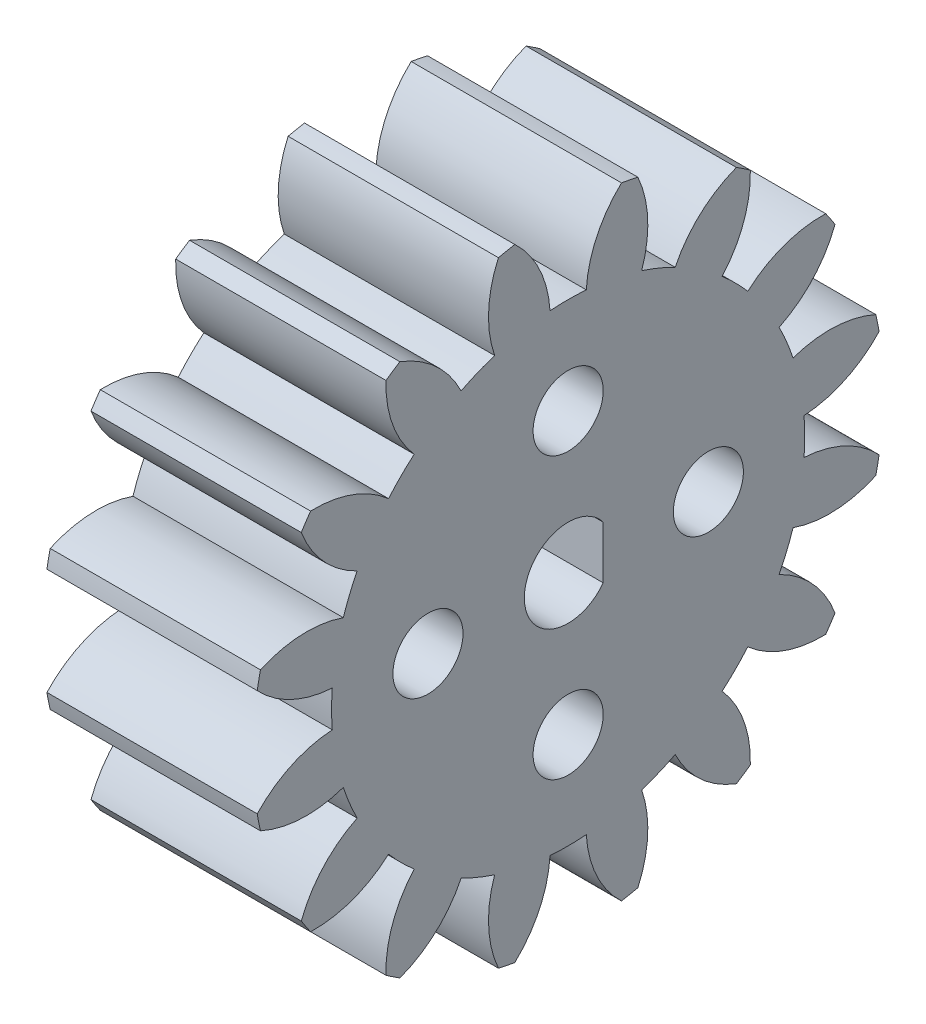
SolidWorks part; units mm, degrees
ref_plane "Plane1" through (0, 0, 0) normal (0, 0, 1) x (1, 0, 0)
ref_plane "Plane2" through (0, 0, 0) normal (0, 1, 0) x (1, 0, 0)
ref_plane "Plane3" through (0, 0, 0) normal (1, 0, 0) x (0, 0, -1)
sketch "HoldingSke" plane through (0, 0, 0) normal (0, 1, 0) x (1, 0, 0)
  line L0 (0, 0) -> (0.4806, -0.1378)
  line L1 (-15, 0) -> (100, 0) construction
  line L2 (0, 0) -> (-2.1039, 2.3779)
  line L3 (0, 0) -> (-11.863, 4.5341)
  line L4 (0, 0) -> (8.3015, 2.3804)
  line L5 (0, 0) -> (-46.8476, -17.4728)
  line L6 (0, 0) -> (-9.9476, -6.7116)
  line L7 (-2.1039, 2.3779) -> (8.6586, 51.2059)
  line L8 (-76.2, 54.61) -> (-75.5, 54.61)
  line L9 (-71.009, 38.7566) -> (-53.1078, 45.2721)
  line L10 (-76.2, 71.12) -> (104.1128, 71.12)
  line L11 (0, 0) -> (-12, 0)
  line L12 (-76.2, 101.6) -> (-76.133, 101.6)
  line L13 (24.9733, 27.94) -> (52.9518, 28.4284)
  line L14 (24.9733, 27.94) -> (24.9743, 27.94)
  line L15 (24.9733, 27.94) -> (100.4006, 29.5858)
  line L16 (-63.627, -2) -> (-12.827, -2)
  circle A0 centre (0, 0) radius 2
  circle A1 centre (0, 0) radius 13.499
  circle A2 centre (0, 0) radius 37.5
  circle A3 centre (0, 0) radius 2
  dimension "MHD" = 26.998
  dimension "Hub_dia" = 75
  dimension "Bore" = 4
  dimension "MBD" = 4
  dimension "Num_teeth" = 16
  dimension "Pitch" = 0.5
  dimension "Overall_len" = 50
  dimension "Show_teeth" = 16
  dimension "Thickness" = 12
  dimension "OAL" = 50.0001
  dimension "T_dim" = 0.7
  dimension "Ap" = 20
  dimension "H" = 19.05
  dimension "Pitch_radius" = 180.3128
  dimension "Width" = 12
  dimension "Backlash" = 0.067
  dimension "Addendum_fac" = 1
  dimension "Dedendum_fac" = 1.25
  dimension "Clearance_fac" = 0.25
  dimension "Dedendum_add" = 0.001
  dimension "Module" = 2
sketch "BasProSke" plane through (0, 0, 0) normal (0, 1, 0) x (1, 0, 0)
  line L0 (-10, 0) -> (60, 0) construction
  line L1 (0, 0) -> (0, 18)
  line L2 (0, 0) -> (12, 0)
  line L3 (12, 0) -> (12, 18)
  line L4 (12, 18) -> (0, 18)
  dimension "Thickness" = 12
  dimension "Diameter" = 36
revolve "Base-Revolve" add sketch "BasProSke" angle 360 about L0
sketch "TooCutSke" plane through (0, 0, 0) normal (1, 0, 0) x (0, 0, -1)
  line L1 (0, 0) -> (0, 107) construction
  line L2 (0, 0) -> (-1.6854, 15.911) construction
  line L3 (0, 0) -> (-6.2172, 31.2558) construction
  line L4 (-1.6854, 15.911) -> (-3.1086, 15.6279) construction
  arc A0 (1.0343, 13.4593) -> (-1.0343, 13.4593) centre (0, 0) ccw
  arc A1 (3.0657, 17.7628) -> (-3.0657, 17.7628) centre (0, 0) ccw
  circle A2 centre (0, 0) radius 16 construction
  circle A3 centre (0, 0) radius 15.0351 construction
  arc A4 (-1.0343, 13.4593) -> (-3.0657, 17.7628) centre (-7.4228, 13.075) ccw
  arc A5 (3.0657, 17.7628) -> (1.0343, 13.4593) centre (7.4228, 13.075) ccw
  dimension "Root_dia" = 26.998
  dimension "Overcut_dia" = 36.0508
  dimension "Pitch_dia" = 32
  dimension "Base_dia" = 30.0702
  dimension "Flank_rad" = 6.4
  dimension "Half_ang" = 11.25
  dimension "Half_CT" = 1.451
extrude "ToothCut" cut sketch "TooCutSke" along normal through all
fillet "Breaks" [suppressed] radius 0.04
fillet "RootFillets" [suppressed] radius 0.501
pattern_circular "TeethCuts" count 16 every 22.5 about axis through (-10, 0, 0) along (1, 0, 0) of "ToothCut", "RootFillets", "Breaks"
sketch "HubNeaOneSke" plane through (0, 0, 0) normal (-1, 0, 0) x (0, 0, 1)
  circle A0 centre (0, 0) radius 13.499
  dimension "Diameter" = 26.998
extrude "HubNearOne" [suppressed] add sketch "HubNeaOneSke" along normal blind 38.0001
sketch "HubNeaBotSke" plane through (0, 0, 0) normal (-1, 0, 0) x (0, 0, 1)
  circle A0 centre (0, 0) radius 13.499
  dimension "Diameter" = 26.998
extrude "HubNearBoth" [suppressed] add sketch "HubNeaBotSke" along normal blind 19
ref_plane "FarPln" through (12, 0, 0) normal (1, 0, 0) x (0, 0, -1)
sketch "HubFarSke" plane through (12, 0, 0) normal (1, 0, 0) x (0, 0, -1)
  circle A0 centre (0, 0) radius 13.499
  dimension "Diameter" = 26.998
extrude "HubFar" [suppressed] add sketch "HubFarSke" along normal blind 19
sketch "BorSke" plane through (0, 0, 0) normal (1, 0, 0) x (0, 0, -1)
  circle A0 centre (0, 0) radius 2
  dimension "Diameter" = 4
extrude "Bore" cut sketch "BorSke" along normal mid plane 100.0001
sketch "KeySke" plane through (0, 0, 0) normal (1, 0, 0) x (0, 0, -1)
  line L0 (-0.8, 0) -> (-0.8, 2.7)
  line L1 (-0.8, 2.7) -> (0.8, 2.7)
  line L2 (0.8, 2.7) -> (0.8, 0)
  line L3 (0, 0) -> (0, 34) construction
  line L4 (-0.8, 0) -> (0.8, 0)
  dimension "Offset" = 2.7
  dimension "Width" = 1.6
extrude "Keyway" [suppressed] cut sketch "KeySke" along normal mid plane 100.0001
pattern_circular "Keyway2" [suppressed] count 2 every 90 about axis through (-10, 0, 0) along (1, 0, 0)
sketch "Sketch1" plane through (12, 0, 0) normal (1, 0, 0) x (0, 0, -1)
  line L0 (-2.5, 0) -> (-2.5, -4.4031) construction
  line L1 (2, 1.5) -> (2, -1.5)
  arc A0 (2, 1.5) -> (2, -1.5) centre (0, 0) ccw
  circle A1 centre (0, 0) radius 8 construction
  circle A2 centre (0, 8) radius 2
  circle A3 centre (0, -8) radius 2
  circle A4 centre (8, 0) radius 2
  circle A5 centre (-8, 0) radius 2
  dimension "D1" = 5
  dimension "D3" = 16
  dimension "D4" = 4
  dimension "D5" = 4
  dimension "D6" = 4
  dimension "D7" = 4
  dimension "D2" = 4.5
extrude "Cut-Extrude1" cut sketch "Sketch1" against normal blind 18
equation "' \"Module@HoldingSke\" = 6.35"
equation "' \"Num_teeth@HoldingSke\" = 12"
equation "' \"Ap@HoldingSke\" =  20"
equation "' \"Ap@HoldingSke\" = 20"
equation "' \"Width@HoldingSke\" = 0.5 * 25.4"
equation "' \"Hub_dia@HoldingSke\"= 1 * 25.4"
equation "' \"Hub_dia@HoldingSke\" = 1 * 25.4"
equation "' \"Overall_len@HoldingSke\" = 1.0 * 25.4"
equation "' \"Bore@HoldingSke\" = 0.75 * 25.4"
equation "' \"T_dim@HoldingSke\" = 0.1 * 25.4"
equation "' \"Width@KeySke\" = 0.25 * 25.4"
equation "' \"Show_teeth@HoldingSke\" = 13"
equation "' \"Backlash@HoldingSke\" = 0.009 * 25.4"
equation "' \"Addendum_fac@HoldingSke\" = 1.0"
equation "' \"Dedendum_fac@HoldingSke\" = 1.25"
equation "' \"Dedendum_add@HoldingSke\" = 0.00005 * 25.4"
equation "' \"Clearance_fac@HoldingSke\" = 0.25"
equation "\"Pitch@HoldingSke\" = 1 / \"Module@HoldingSke\""
equation "\"Overcut_dia@TooCutSke\" = (\"Num_teeth@HoldingSke\" + 2 * \"Addendum_fac@HoldingSke\") / \"Pitch@HoldingSke\" + 0.002 * 25.4"
equation "\"Pitch_dia@TooCutSke\" = \"Num_teeth@HoldingSke\" / \"Pitch@HoldingSke\""
equation "\"Base_dia@TooCutSke\" = \"Num_teeth@HoldingSke\" / \"Pitch@HoldingSke\" * cos((\"Ap@HoldingSke\"  * 3.14159265 / 180))"
equation "\"Root_dia@TooCutSke\" = (\"Num_teeth@HoldingSke\" + 2) / \"Pitch@HoldingSke\" - 2 * (\"Addendum_fac@HoldingSke\" + \"Dedendum_fac@HoldingSke\") / \"Pitch@HoldingSke\" - \"Dedendum_add@HoldingSke\" * 2"
equation "\"Half_ang@TooCutSke\" = 180 / \"Num_teeth@HoldingSke\""
equation "\"Half_CT@TooCutSke\" = \"Num_teeth@HoldingSke\" / \"Pitch@HoldingSke\" * sin((3.14159265 / 2 / \"Num_teeth@HoldingSke\")) / 2 - 7 * \"Backlash@HoldingSke\" / 4"
equation "\"Flank_rad@TooCutSke\" = \"Num_teeth@HoldingSke\" / \"Pitch@HoldingSke\" / 5"
equation "\"Radius@RootFillets\" = \"Clearance_fac@HoldingSke\" / \"Pitch@HoldingSke\" + \"Dedendum_add@HoldingSke\""
equation "\"Break_rad@Breaks\" = 0.02 / \"Pitch@HoldingSke\""
equation "\"Thickness@HoldingSke\" = \"Width@HoldingSke\""
equation "\"OAL@HoldingSke\" = \"Thickness@HoldingSke\""
equation "\"MHD@HoldingSke\" = (\"Num_teeth@HoldingSke\" + 2) / \"Pitch@HoldingSke\" - 2 * (\"Addendum_fac@HoldingSke\" + \"Dedendum_fac@HoldingSke\")  / \"Pitch@HoldingSke\" - \"Dedendum_add@HoldingSke\" * 2"
equation "\"MBD@HoldingSke\" = (\"Num_teeth@HoldingSke\" + 2) / \"Pitch@HoldingSke\" - 2 * (\"Addendum_fac@HoldingSke\" + \"Dedendum_fac@HoldingSke\")  / \"Pitch@HoldingSke\" - \"Dedendum_add@HoldingSke\" * 2 - 0.002 * 25.4"
equation "\"MHD@HoldingSke\" = ((sgn( \"MHD@HoldingSke\" - \"Hub_dia@HoldingSke\" )-1)*( \"MHD@HoldingSke\" - \"Hub_dia@HoldingSke\" ))/-2+ \"Hub_dia@HoldingSke\""
equation "\"MBD@HoldingSke\" = ((sgn( \"MBD@HoldingSke\" - \"Bore@HoldingSke\" )-1)*( \"MBD@HoldingSke\" - \"Bore@HoldingSke\" ))/-2+ \"Bore@HoldingSke\""
equation "\"OAL@HoldingSke\" = ((sgn( \"OAL@HoldingSke\" - \"Overall_len@HoldingSke\" )+1)*( \"OAL@HoldingSke\" - \"Overall_len@HoldingSke\" ))/2 + \"Overall_len@HoldingSke\" + 0.000002 * 25.4"
equation "\"Num_teeth@TeethCuts\" = int( \"Show_teeth@HoldingSke\" ) + 1"
equation "\"Num_teeth@TeethCuts\" = ((sgn( \"Num_teeth@TeethCuts\" - \"Num_teeth@HoldingSke\" )-1)*( \"Num_teeth@TeethCuts\" - \"Num_teeth@HoldingSke\" ))/-2+ \"Num_teeth@HoldingSke\""
equation "\"Num_teeth@TeethCuts\" = ((sgn( \"Num_teeth@TeethCuts\" - 2.0)+1)*( \"Num_teeth@TeethCuts\" - 2.0))/2 +2.0"
equation "\"Angle@TeethCuts\" = 360.0 / \"Num_teeth@HoldingSke\""
equation "\"Diameter@BasProSke\" = (\"Num_teeth@HoldingSke\" + 2 * \"Addendum_fac@HoldingSke\") / \"Pitch@HoldingSke\""
equation "\"Thickness@BasProSke\"  = \"Thickness@HoldingSke\""
equation "' \"Fillet_rad@BasProSke\" =  \"Thickness@HoldingSke\" * 0.05"
equation "' \"Fillet_rad@BasProSke\" = \"Thickness@HoldingSke\" * 0.05"
equation "\"MHD@HoldingSke\" = ((sgn( \"MHD@HoldingSke\" - \"Root_dia@TooCutSke\" )-1)*( \"MHD@HoldingSke\" - \"Root_dia@TooCutSke\" ))/-2+ \"Root_dia@TooCutSke\""
equation "\"Diameter@HubNeaOneSke\" = \"MHD@HoldingSke\""
equation "\"Length@HubNearOne\" = \"OAL@HoldingSke\" - \"Thickness@BasProSke\""
equation "\"Diameter@HubNeaBotSke\" = \"MHD@HoldingSke\""
equation "\"Length@HubNearBoth\" = ( \"OAL@HoldingSke\" - \"Thickness@BasProSke\" ) / 2.0"
equation "\"Thickness@FarPln\" = \"Thickness@BasProSke\""
equation "\"Diameter@HubFarSke\" = \"MHD@HoldingSke\""
equation "\"Length@HubFar\" = ( \"OAL@HoldingSke\" - \"Thickness@BasProSke\" ) / 2.0"
equation "\"Diameter@BorSke\" = \"MBD@HoldingSke\""
equation "\"D1@Bore\" = \"OAL@HoldingSke\" * 2.0"
equation "\"D1@Keyway\" = \"OAL@HoldingSke\" * 2.0"
equation "\"Offset@KeySke\" = \"T_dim@HoldingSke\" + \"MBD@HoldingSke\" / 2.0"
